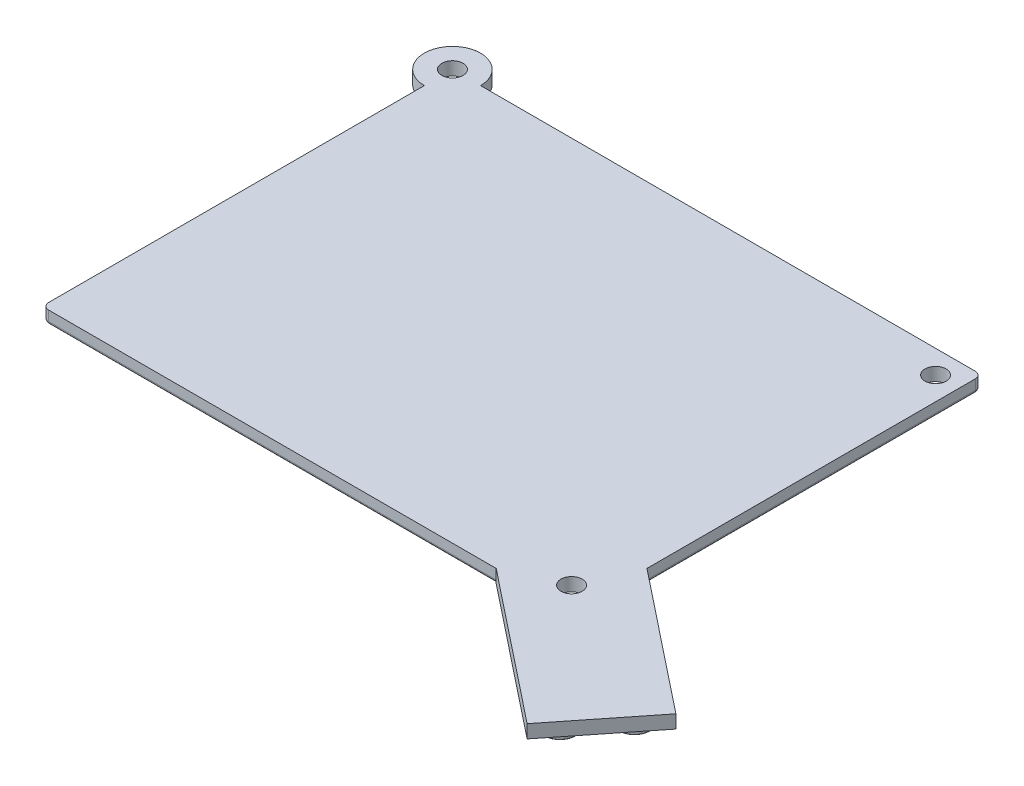
SolidWorks part; units mm, degrees
material "PVC Rigid"
ref_plane "Front Plane" through (0, 0, 0) normal (0, 0, 1) x (1, 0, 0)
ref_plane "Top Plane" through (0, 0, 0) normal (0, 1, 0) x (1, 0, 0)
ref_plane "Right Plane" through (0, 0, 0) normal (1, 0, 0) x (0, 0, -1)
sketch "Sketch1" plane through (0, 0, 0) normal (0, 1, 0) x (1, 0, 0)
  line L0 (40, -31) -> (-40, 31) construction
  line L1 (-40, -31) -> (40, -31)
  line L2 (-40, -31) -> (-40, 26.75)
  line L3 (-35.75, 31) -> (40, 31)
  line L4 (40, -31) -> (40, 31)
  line L5 (-40, -31) -> (40, 31) construction
  arc A5 (-35.75, 31) -> (-40, 26.75) centre (-40, 31) ccw
  point P0 (0, 0)
  dimension "D3" = 4.25
  dimension "D4" = 4.25
  dimension "D5" = 4.25
  dimension "D1" = 80
  dimension "D2" = 62
extrude "Main Body" add sketch "Sketch1" along normal blind 2
fillet "Corners" radius 1 3 edges at (-40, 1, 31) (40, 1, -31) (40, 1, 31)
fillet "Edge" radius 0.5 7 edges at (-39.7071, 0, 30.7071) (39.7071, 0, -30.7071) (39.7071, 0, 30.7071) (-40, 0, 1.625) (1.625, 0, -31) (40, 0, 0) (0, 0, 31)
sketch "Sketch8" plane through (0, 2, 0) normal (0, 1, 0) x (1, 0, 0)
  line L2 (40, -19.6117) -> (61.2107, -36.4473)
  line L3 (40, -30) -> (40, 30) construction
  line L5 (61.2107, -36.4473) -> (51.2636, -48.9794)
  line L6 (51.2636, -48.9794) -> (28.6117, -31)
  line L8 (-39, -31) -> (39, -31) construction
  line L9 (28.6117, -31) -> (40, -19.6117)
  line L10 (39, -30) -> (24.8579, -15.8579) construction
  line L11 (39, -30.5) -> (-39, -30.5) construction
  point P13 (34.3059, -25.3059)
  dimension "D1" = 45
  dimension "D2" = 20
  dimension "D3" = 16
  dimension "D4" = 28
extrude "DivingBoard" add sketch "Sketch8" against normal up to surface (2 mm away) up to face at (-0.2552, 0, -0.2552)
sketch "Sketch7" plane through (0, 0, 0) normal (0, -1, 0) x (-1, 0, 0)
  line L0 (39, -31) -> (-28.6117, -31) construction
  line L3 (-40, -19.6117) -> (-40, 30) construction
  line L4 (-39, 31) -> (35.75, 31) construction
  circle A0 centre (40, 31) radius 1.6
  circle A2 centre (-36.5, -27.5) radius 1.6
  circle A3 centre (-36.5, 27.5) radius 1.6
  arc A4 (39.5, 26.7795) -> (35.7795, 30.5) centre (40, 31) ccw construction
  dimension "D1" = 3.2
  dimension "D4" = 3.2
  dimension "D5" = 3.2
  dimension "D2" = 3.5
  dimension "D3" = 3.5
  dimension "D6" = 3.5
extrude "Lid Holes" cut sketch "Sketch7" against normal through all both and the other way through all
sketch "Sketch4" plane through (0, 0, 0) normal (0, -1, 0) x (-1, 0, 0)
  line L0 (-30, 24) -> (-30, -24) construction
  line L3 (-1.1, 0) -> (1.1, 0) construction
  line L4 (-40, -19.6117) -> (-40, 30) construction
  circle A0 centre (-30, 24) radius 2.325
  circle A1 centre (-30, 16) radius 2.325
  point P2 (-30, 0)
  dimension "D1" = 4.65
  dimension "D2" = 4.65
  dimension "D3" = 8
  dimension "D4" = 48
  dimension "D5" = 10
extrude "Boss-Extrude3" add sketch "Sketch4" along normal blind 1.6
fillet "Fillet3" radius 0.05 1 edges at (30, -1.6, -26.325)
pattern_linear "LPattern5" count 4 spacing 8 along (-1, 0, 0) of "Boss-Extrude3", "Fillet3"
sketch "LEGO straightline reference" plane through (0, 0, 0) normal (0, -1, 0) x (-1, 0, 0)
  line L0 (-30, 24) -> (-30, 16) construction
  line L1 (-30, 16) -> (-30, 20) construction
  line L2 (-30, 20) -> (-6, 20) construction
  line L3 (-6, 24) -> (-6, 16) construction
  point P10 (-18, 20)
sketch "Sketch10" plane through (0, 0, 0) normal (0, -1, 0) x (-1, 0, 0)
  line L0 (-56.2371, -42.7133) -> (-31.1728, -22.8191) construction
  line L1 (-61.2107, -36.4473) -> (-51.2636, -48.9794) construction
  line L2 (-55.5909, -37.0935) -> (-50.6173, -43.3596) construction
  circle A0 centre (-55.5909, -37.0935) radius 2.325
  circle A1 centre (-50.6173, -43.3596) radius 2.325
  point P5 (-56.2371, -42.7133)
  point P9 (-53.1041, -40.2266)
  dimension "D2" = 4.65
  dimension "D3" = 4.65
  dimension "D1" = 32
  dimension "D4" = 8
  dimension "D5" = 4
extrude "Pegs (Diagonal)" add sketch "Sketch10" along normal blind 1.6
fillet "Fillet4" radius 0.05 2 edges at (50.6173, -1.6, 41.0346) (55.5909, -1.6, 34.7685)
pattern_linear "LPattern6" count 4 spacing 8 along (-0.7833, 0, -0.6217) of "Fillet4", "Pegs (Diagonal)"
equation "\"D3@Sketch7\"=\"D2@Sketch7\""
equation "\"D4@Sketch7\"=\"D1@Sketch7\""
equation "\"D5@Sketch7\"=\"D1@Sketch7\""
equation "\"D2@Sketch4\"=\"D1@Sketch4\""
equation "\"D3@Sketch10\"=\"D2@Sketch10\""
